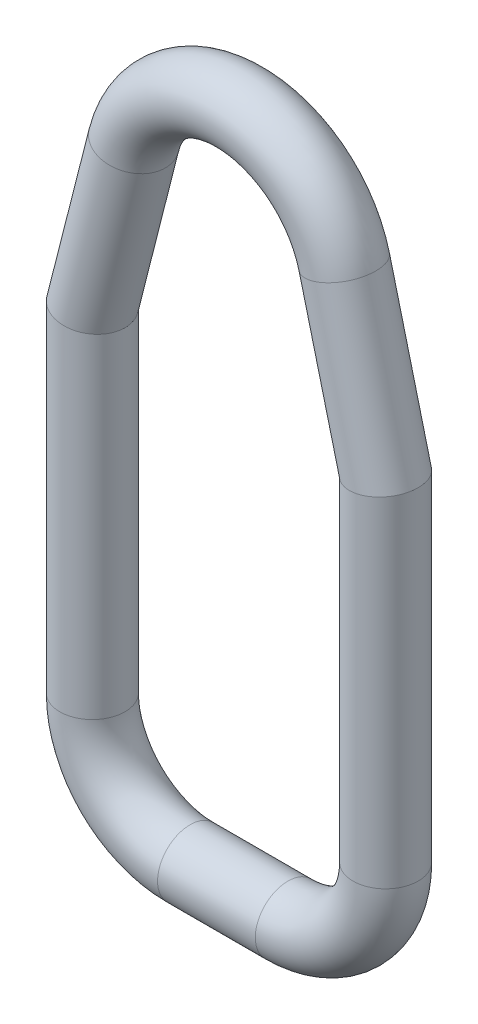
SolidWorks part; units mm, degrees
ref_plane "Plane1" through (0, 0, 0) normal (0, 0, 1) x (1, 0, 0)
ref_plane "Plane2" through (0, 0, 0) normal (0, 1, 0) x (1, 0, 0)
ref_plane "Plane3" through (0, 0, 0) normal (1, 0, 0) x (0, 0, -1)
sketch "Sketch1" plane through (0, 0, 0) normal (0, 0, 1) x (1, 0, 0)
  line L0 (-1.143, 0) -> (1.143, 0)
  line L1 (-3.429, 2.286) -> (-3.429, 10.16)
  line L2 (-3.429, 10.16) -> (-2.4615, 13.9615)
  line L3 (2.4615, 13.9615) -> (3.429, 10.16)
  line L4 (3.429, 10.16) -> (3.429, 2.286)
  arc A0 (2.4615, 13.9615) -> (-2.4615, 13.9615) centre (0, 13.335) ccw
  arc A1 (-1.143, 0) -> (-3.429, 2.286) centre (-1.143, 2.286) cw
  arc A2 (3.429, 2.286) -> (1.143, 0) centre (1.143, 2.286) cw
  dimension "D1" = 2.54
  dimension "D2" = 2.286
  dimension "D3" = 6.858
  dimension "D4" = 15.875
  dimension "D5" = 10.16
sketch "Sketch2" plane through (0, 0, 0) normal (1, 0, 0) x (0, 0, -1)
  circle A0 centre (0, 0) radius 0.762
  dimension "D1" = 1.524
sweep "Base-Sweep" add profiles "Sketch2" path "Sketch1"
